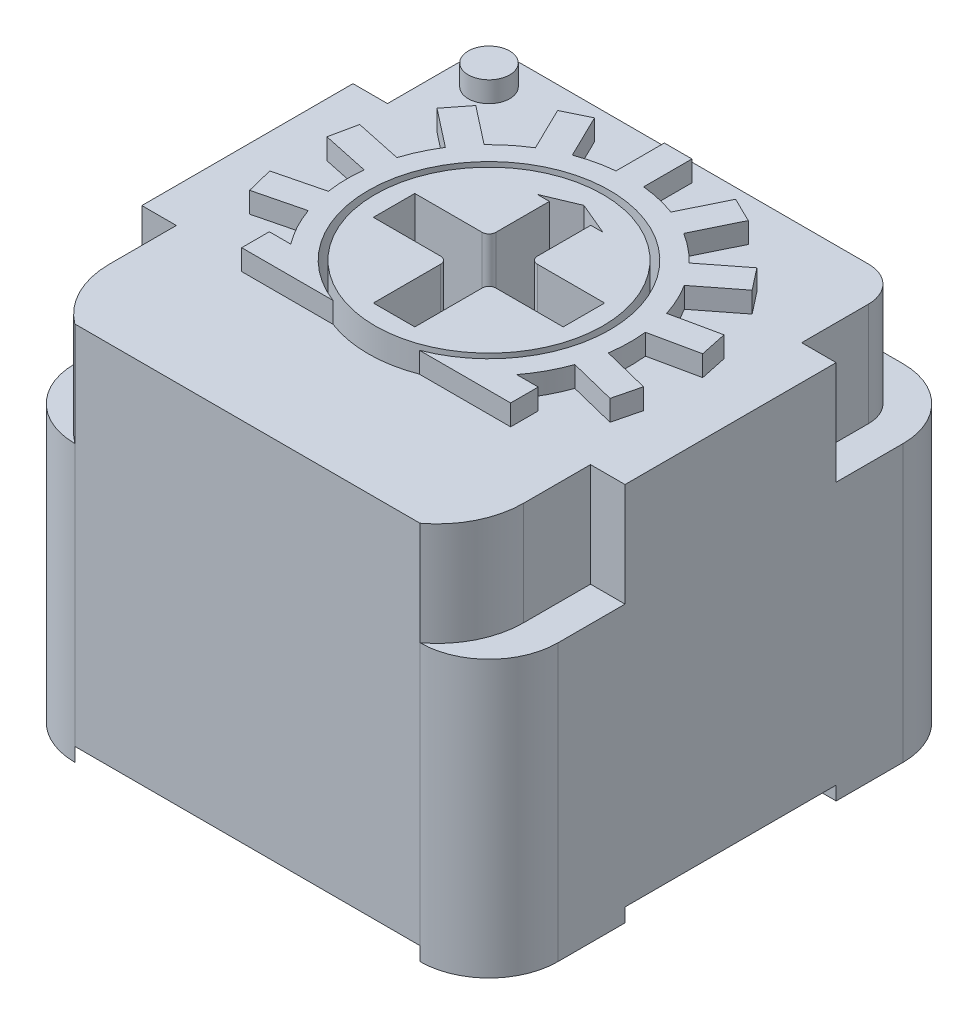
SolidWorks part; units mm, degrees
ref_plane "Front Plane" through (0, 0, 0) normal (0, 0, 1) x (1, 0, 0)
ref_plane "Top Plane" through (0, 0, 0) normal (0, 1, 0) x (1, 0, 0)
ref_plane "Right Plane" through (0, 0, 0) normal (1, 0, 0) x (0, 0, -1)
sketch "Sketch1" plane through (0, 0, 0) normal (0, 1, 0) x (1, 0, 0)
  line L1 (2.5, -3.5) -> (-2.5, -3.5)
  line L2 (3.5, -2.5) -> (3.5, 2.5)
  line L3 (2.5, 3.5) -> (-2.5, 3.5)
  line L4 (-3.5, -2.5) -> (-3.5, 2.5)
  line L5 (3.5, -3.5) -> (-3.5, 3.5) construction
  line L6 (3.5, 3.5) -> (-3.5, -3.5) construction
  arc A0 (-2.5, 3.5) -> (-3.5, 2.5) centre (-2.5, 2.5) ccw
  arc A1 (3.5, 2.5) -> (2.5, 3.5) centre (2.5, 2.5) ccw
  arc A2 (3.5, -2.5) -> (2.5, -3.5) centre (2.5, -2.5) cw
  arc A3 (-2.5, -3.5) -> (-3.5, -2.5) centre (-2.5, -2.5) cw
  point P0 (0, 0)
  dimension "D2" = 1
  dimension "D3" = 1
  dimension "D4" = 1
  dimension "D1" = 7
extrude "Boss-Extrude1" add sketch "Sketch1" along normal blind 5.5
sketch "Sketch3" plane through (0, 5.5, 0) normal (0, 1, 0) x (1, 0, 0)
  circle A0 centre (0, 0) radius 1.75
  dimension "D1" = 3.5
extrude "Cut-Extrude1" cut sketch "Sketch3" against normal blind 1.75
sketch "Sketch4" plane through (0, 3.75, 0) normal (0, 1, 0) x (1, 0, 0)
  circle A0 centre (0, 0) radius 1.65
  circle A1 centre (0, 0) radius 1.75 construction
  dimension "D1" = 0.1
extrude "Boss-Extrude2" add sketch "Sketch4" along normal offset from surface (2.05 mm away) 5.8 separate body up to face at (0, 0, 0)
sketch "Sketch5" plane through (0, 5.8, 0) normal (0, 1, 0) x (1, 0, 0)
  line L0 (-0.3, 0.3) -> (-0.3, 1.175)
  line L1 (1.375, -0.3) -> (0.3, -0.3)
  line L2 (1.375, -0.3) -> (1.375, 0.3)
  line L3 (1.375, 0.3) -> (0.3, 0.3)
  line L4 (-1.375, -0.3) -> (-1.375, 0.3)
  line L5 (1.375, -0.3) -> (-1.375, 0.3) construction
  line L6 (1.375, 0.3) -> (-1.375, -0.3) construction
  line L7 (0.3, -1.375) -> (-0.3, -1.375)
  line L8 (0.3, -1.375) -> (0.3, -0.3)
  line L10 (-0.3, -1.375) -> (-0.3, -0.3)
  line L11 (0.3, -1.375) -> (-0.2748, 1.2593) construction
  line L12 (0.2748, 1.2593) -> (-0.3, -1.375) construction
  line L13 (-0.3, -0.3) -> (-1.375, -0.3)
  line L14 (0.3, 0.3) -> (0.3, 1.175)
  line L15 (-0.3, 0.3) -> (-1.375, 0.3)
  line L16 (0, 1.375) -> (-0.475, 1.175)
  line L17 (-0.475, 1.175) -> (-0.3, 1.175)
  line L18 (0.475, 1.175) -> (0, 1.375)
  line L19 (-0.3, 0.3) -> (0.3, 0.3) construction
  line L20 (0.3, 1.175) -> (0.475, 1.175)
  line L21 (0, 0.3) -> (0, 1.375) construction
  point P0 (0, 0)
  point P6 (0, 0)
  dimension "D1" = 2.75
  dimension "D2" = 0.6
  dimension "D3" = 0.95
  dimension "D4" = 0.2
extrude "Cut-Extrude2" cut sketch "Sketch5" against normal blind 1.6
fillet "Fillet1" radius 0.1 4 edges at (0.3, 5, 0.3) (-0.3, 5, 0.3) (0.3, 5, -0.3) (-0.3, 5, -0.3)
sketch "Sketch6" plane through (0, 5.5, 0) normal (0, 1, 0) x (1, 0, 0)
  line L0 (-0.625, -1.6346) -> (-1.948, -1.6346)
  line L1 (-1.948, -1.6346) -> (-1.948, -1.2346)
  line L2 (-1.948, -1.2346) -> (-1.6365, -1.2346)
  line L3 (0.625, -1.6346) -> (1.948, -1.6346)
  line L4 (1.948, -1.6346) -> (1.948, -1.2346)
  line L5 (1.948, -1.2346) -> (1.6365, -1.2346)
  line L6 (-1.948, -1.6346) -> (0, 0) construction
  line L7 (0, 0) -> (1.948, -1.6346) construction
  line L8 (-1.9312, -0.6876) -> (-2.6104, -0.857)
  line L9 (-2.6104, -0.857) -> (-2.7072, -0.4689)
  line L10 (-2.7072, -0.4689) -> (-2.028, -0.2995)
  line L11 (-2.7219, 0.3741) -> (-2.0372, 0.2286)
  line L12 (-2.7219, 0.3741) -> (-2.6388, 0.7654)
  line L13 (-2.6388, 0.7654) -> (-1.9541, 0.6198)
  line L14 (-2.2825, 1.5294) -> (-1.7308, 1.0985)
  line L15 (-2.2825, 1.5294) -> (-2.0362, 1.8447)
  line L16 (-2.0362, 1.8447) -> (-1.4846, 1.4137)
  line L17 (-1.381, 2.3752) -> (-1.0741, 1.7461)
  line L18 (-1.381, 2.3752) -> (-1.0215, 2.5506)
  line L19 (-1.0215, 2.5506) -> (-0.7146, 1.9214)
  line L20 (-0.2, 2.0402) -> (-0.2, 2.7402)
  line L21 (-0.2, 2.7402) -> (0.2, 2.7402)
  line L22 (0.2, 2.7402) -> (0.2, 2.0402)
  line L23 (0, 0) -> (0, 2.7402) construction
  line L24 (-2.6588, -0.6629) -> (0, 0) construction
  line L25 (0, 0) -> (-2.6803, 0.5697) construction
  line L26 (0, 0) -> (-2.1593, 1.687) construction
  line L27 (0, 0) -> (-1.2012, 2.4629) construction
  line L28 (1.0215, 2.5506) -> (0.7146, 1.9214)
  line L29 (1.381, 2.3752) -> (1.0215, 2.5506)
  line L30 (1.381, 2.3752) -> (1.0741, 1.7461)
  line L31 (2.0362, 1.8447) -> (1.4846, 1.4137)
  line L32 (2.2825, 1.5294) -> (2.0362, 1.8447)
  line L33 (2.2825, 1.5294) -> (1.7308, 1.0985)
  line L34 (2.6388, 0.7654) -> (1.9541, 0.6198)
  line L35 (2.7219, 0.3741) -> (2.6388, 0.7654)
  line L36 (2.7219, 0.3741) -> (2.0372, 0.2286)
  line L37 (2.7072, -0.4689) -> (2.028, -0.2995)
  line L38 (2.6104, -0.857) -> (2.7072, -0.4689)
  line L39 (1.9312, -0.6876) -> (2.6104, -0.857)
  arc A0 (-0.625, -1.6346) -> (0.625, -1.6346) centre (0, 0) cw
  circle A1 centre (0, 0) radius 1.75 construction
  arc A2 (-1.6365, -1.2346) -> (-1.9312, -0.6876) centre (0, 0) cw
  arc A3 (-2.028, -0.2995) -> (-2.0372, 0.2286) centre (0, 0) cw
  arc A4 (-1.9541, 0.6198) -> (-1.7308, 1.0985) centre (0, 0) cw
  arc A5 (-1.4846, 1.4137) -> (-1.0741, 1.7461) centre (0, 0) cw
  arc A6 (-0.7146, 1.9214) -> (-0.2, 2.0402) centre (0, 0) cw
  arc A7 (0.2, 2.0402) -> (0.7146, 1.9214) centre (0, 0) cw
  arc A8 (1.0741, 1.7461) -> (1.4846, 1.4137) centre (0, 0) cw
  arc A9 (1.9312, -0.6876) -> (1.6365, -1.2346) centre (0, 0) cw
  arc A10 (2.0372, 0.2286) -> (2.028, -0.2995) centre (0, 0) cw
  arc A11 (1.7308, 1.0985) -> (1.9541, 0.6198) centre (0, 0) cw
  dimension "D1" = 0.3
  dimension "D2" = 1.25
  dimension "D3" = 260
  dimension "D4" = 0.4
  dimension "D5" = 26
  dimension "D6" = 52
  dimension "D7" = 78
  dimension "D8" = 104
  dimension "D9" = 0.7
extrude "Boss-Extrude3" add sketch "Sketch6" along normal up to surface (0.3 mm away) up to face at (0, 5.8, -0.175)
sketch "Sketch7" plane through (0, 5.5, 0) normal (0, 1, 0) x (1, 0, 0)
  line L0 (0, 0) -> (-2.4749, 2.4749) construction
  line L1 (-2.4749, 2.4749) -> (0, 0) construction
  line L2 (0, 0) -> (0, 3.5) construction
  line L3 (2.5, 3.5) -> (-2.5, 3.5) construction
  circle A0 centre (-2.4749, 2.4749) radius 0.3
  dimension "D1" = 0.6
  dimension "D2" = 45
  dimension "D3" = 3.5
extrude "Boss-Extrude4" add sketch "Sketch7" along normal up to surface (0.3 mm away) up to face at (0, 5.8, -0.6779)
sketch "Sketch2" plane through (0, 5.5, 0) normal (0, 1, 0) x (1, 0, 0)
  line L0 (3.5, -2.5) -> (3.5, 2.5) construction
  line L1 (-2.5, -3.5) -> (2.5, -3.5) construction
  line L2 (2.5, 3.5) -> (-2.5, 3.5) construction
  line L3 (-3.5, 2.5) -> (-3.5, -2.5) construction
  line L4 (3.5, -2.5) -> (3.5, 2.5)
  line L5 (-2.5, -3.5) -> (2.5, -3.5)
  line L6 (2.5, 3.5) -> (-2.5, 3.5)
  line L7 (-3.5, 2.5) -> (-3.5, -2.5)
  line L8 (-3.5, 1.5294) -> (-3, 1.5294)
  line L9 (-3, 1.5294) -> (-3, 3)
  line L10 (-3, 3) -> (3, 3)
  line L11 (3, 3) -> (3, 1.5294)
  line L12 (3, 1.5294) -> (3.5, 1.5294)
  line L13 (0, 3) -> (0, 3.5) construction
  line L14 (-3.5, -1.5294) -> (-3, -1.5294)
  line L15 (-3, -1.5294) -> (-3, -2.5)
  line L16 (-3, -1.5294) -> (-3, 1.5294) construction
  line L17 (3.5, -1.5294) -> (3, -1.5294)
  line L18 (3, -1.5294) -> (3, -2.5)
  arc A0 (2.5, -3.5) -> (3.5, -2.5) centre (2.5, -2.5) ccw construction
  arc A1 (-3.5, -2.5) -> (-2.5, -3.5) centre (-2.5, -2.5) ccw construction
  arc A2 (3.5, 2.5) -> (2.5, 3.5) centre (2.5, 2.5) ccw construction
  arc A3 (-2.5, 3.5) -> (-3.5, 2.5) centre (-2.5, 2.5) ccw construction
  arc A4 (2.5, -3.5) -> (3.5, -2.5) centre (2.5, -2.5) ccw
  arc A5 (-3.5, -2.5) -> (-2.5, -3.5) centre (-2.5, -2.5) ccw
  arc A6 (3.5, 2.5) -> (2.5, 3.5) centre (2.5, 2.5) ccw
  arc A7 (-2.5, 3.5) -> (-3.5, 2.5) centre (-2.5, 2.5) ccw
  arc A8 (-3, -2.5) -> (-2.5, -3.5) centre (-1.75, -2.5) ccw
  arc A9 (2.5, -3.5) -> (3, -2.5) centre (1.75, -2.5) ccw
  point P25 (-3, 0)
  dimension "D1" = 0.5
extrude "Cut-Extrude3" cut sketch "Sketch2" against normal blind 1.5 contours A8 L15 L14 L7 A5 | A9 A4 L4 L17 L18 | L6 A7 L7 L8 L9 L10 L11 L12 L4 A6
fillet "Fillet2" radius 0.5 2 edges at (3, 4.75, -3) (-3, 4.75, -3)
sketch "Sketch10" plane through (0, 0, 0) normal (0, 1, 0) x (1, 0, 0)
  line L0 (3.5, -2.5) -> (3.5, -1.5294) construction
  line L1 (3.5, -1.5294) -> (3, -1.5294) construction
  line L2 (3, -1.5294) -> (3, -2.5) construction
  line L3 (-3, -2.5) -> (-3, -1.5294) construction
  line L4 (-3, -1.5294) -> (-3.5, -1.5294) construction
  line L5 (-3.5, -1.5294) -> (-3.5, -2.5) construction
  line L6 (2.5, 3.5) -> (-2.5, 3.5) construction
  line L7 (-3.5, 2.5) -> (-3.5, 1.5294) construction
  line L8 (-3.5, 1.5294) -> (-3, 1.5294) construction
  line L9 (-3, 1.5294) -> (-3, 2.5) construction
  line L10 (-2.5, 3) -> (2.5, 3) construction
  line L11 (3, 2.5) -> (3, 1.5294) construction
  line L12 (3, 1.5294) -> (3.5, 1.5294) construction
  line L13 (3.5, 1.5294) -> (3.5, 2.5) construction
  line L14 (3.5, -2.5) -> (3.5, -1.5294)
  line L15 (3.5, -1.5294) -> (3, -1.5294)
  line L16 (3, -1.5294) -> (3, -2.5)
  line L17 (-3, -2.5) -> (-3, -1.5294)
  line L18 (-3, -1.5294) -> (-3.5, -1.5294)
  line L19 (-3.5, -1.5294) -> (-3.5, -2.5)
  line L20 (2.5, 3.5) -> (-2.5, 3.5)
  line L21 (-3.5, 2.5) -> (-3.5, 1.5294)
  line L22 (-3.5, 1.5294) -> (-3, 1.5294)
  line L23 (-3, 1.5294) -> (-3, 2.5)
  line L24 (-2.5, 3) -> (2.5, 3)
  line L25 (3, 2.5) -> (3, 1.5294)
  line L26 (3, 1.5294) -> (3.5, 1.5294)
  line L27 (3.5, 1.5294) -> (3.5, 2.5)
  line L28 (-2.5, -3.5) -> (2.5, -3.5)
  line L29 (3.5, -1.5294) -> (3.5, 1.5294)
  line L30 (-3.5, -1.5294) -> (-3.5, 1.5294)
  arc A0 (2.5, -3.5) -> (3, -2.5) centre (1.75, -2.5) ccw construction
  arc A1 (2.5, -3.5) -> (3.5, -2.5) centre (2.5, -2.5) ccw construction
  arc A2 (-3, -2.5) -> (-2.5, -3.5) centre (-1.75, -2.5) ccw construction
  arc A3 (-3.5, -2.5) -> (-2.5, -3.5) centre (-2.5, -2.5) ccw construction
  arc A4 (-2.5, 3.5) -> (-3.5, 2.5) centre (-2.5, 2.5) ccw construction
  arc A5 (-2.5, 3) -> (-3, 2.5) centre (-2.5, 2.5) ccw construction
  arc A6 (3, 2.5) -> (2.5, 3) centre (2.5, 2.5) ccw construction
  arc A7 (3.5, 2.5) -> (2.5, 3.5) centre (2.5, 2.5) ccw construction
  arc A8 (2.5, -3.5) -> (3, -2.5) centre (1.75, -2.5) ccw
  arc A9 (2.5, -3.5) -> (3.5, -2.5) centre (2.5, -2.5) ccw
  arc A10 (-3, -2.5) -> (-2.5, -3.5) centre (-1.75, -2.5) ccw
  arc A11 (-3.5, -2.5) -> (-2.5, -3.5) centre (-2.5, -2.5) ccw
  arc A12 (-2.5, 3.5) -> (-3.5, 2.5) centre (-2.5, 2.5) ccw
  arc A13 (-2.5, 3) -> (-3, 2.5) centre (-2.5, 2.5) ccw
  arc A14 (3, 2.5) -> (2.5, 3) centre (2.5, 2.5) ccw
  arc A15 (3.5, 2.5) -> (2.5, 3.5) centre (2.5, 2.5) ccw
extrude "Cut-Extrude7" cut sketch "Sketch10" along normal blind 0.2 contours L25 A14 L24 A13 L23 L22 L30 L18 L17 A10 L28 A8 L16 L15 L29 L26
sketch "Sketch11" plane through (0, 0.2, 0) normal (0, -1, 0) x (1, 0, 0)
  line L0 (3.5, 0) -> (2.5, 0) construction
  line L1 (3.5, 1.5294) -> (3.5, -1.5294) construction
  line L2 (2.5, 0) -> (0, 0) construction
  line L3 (-2.5, 0) -> (-3.5, 0) construction
  line L4 (-3.5, 1.5294) -> (-3.5, -1.5294) construction
  line L5 (0, 0) -> (0, -2.5) construction
  line L6 (0, 0) -> (-2.5, 0) construction
  circle A0 centre (2.5, 0) radius 0.225
  circle A1 centre (0, -2.5) radius 0.225
  circle A2 centre (-2.5, 0) radius 0.225
  dimension "D1" = 0.45
  dimension "D2" = 2.5
extrude "Boss-Extrude6" add sketch "Sketch11" along normal blind 7.2 separate body
sketch "Skizze2" plane through (0, -7, 0) normal (0, -1, 0) x (1, 0, 0)
  line L1 (-7.1973, 3.8182) -> (4.4279, 3.8182)
  line L2 (-7.1973, 3.8182) -> (-7.1973, -6.5682)
  line L3 (-7.1973, -6.5682) -> (4.4279, -6.5682)
  line L4 (4.4279, 3.8182) -> (4.4279, -6.5682)
extrude "Schnitt-Linear austragen1" cut sketch "Skizze2" against normal blind 7
